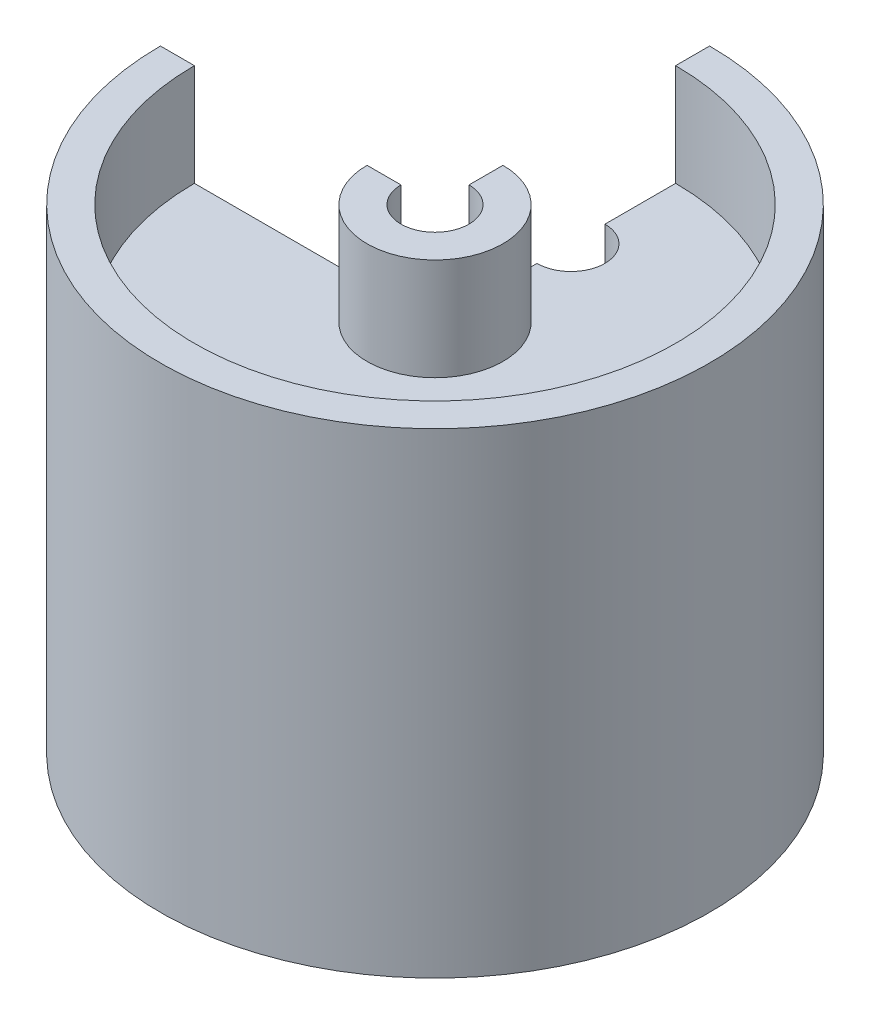
SolidWorks part; units mm, degrees
ref_plane "Front Plane" through (0, 0, 0) normal (0, 0, 1) x (1, 0, 0)
ref_plane "Top Plane" through (0, 0, 0) normal (0, 1, 0) x (1, 0, 0)
ref_plane "Right Plane" through (0, 0, 0) normal (1, 0, 0) x (0, 0, -1)
sketch "Sketch1" plane through (0, 0, 0) normal (1, 0, 0) x (0, 0, -1)
  line L3 (22.479, 35.4984) -> (22.479, 45.0234)
  line L4 (22.479, 45.0234) -> (25.654, 45.0234)
  line L5 (25.654, 45.0234) -> (25.654, 0.5734)
  line L6 (25.654, 0.5734) -> (22.479, 0.5734)
  line L7 (22.479, 0.5734) -> (22.479, 32.3234)
  line L8 (22.479, 32.3234) -> (6.35, 32.3234)
  line L12 (0, 45.0234) -> (0, 0) construction
  line L13 (22.479, 35.4984) -> (6.35, 35.4984)
  line L14 (6.35, 35.4984) -> (6.35, 45.0234)
  line L15 (6.35, 45.0234) -> (3.175, 45.0234)
  line L16 (3.175, 45.0234) -> (3.175, 0.5734)
  line L17 (3.175, 0.5734) -> (6.35, 0.5734)
  line L19 (6.35, 32.3234) -> (6.35, 0.5734)
  dimension "D1" = 44.45
  dimension "D2" = 16.129
  dimension "D3" = 3.175
  dimension "D4" = 31.75
  dimension "D5" = 16.129
  dimension "D6" = 9.525
  dimension "D7" = 3.175
revolve "Revolve2" add sketch "Sketch1" angle 270 about L12
sketch "Sketch5" plane through (0, 0, 0) normal (0, 1, 0) x (1, 0, 0)
  circle A0 centre (0, 12.7) radius 3.175
  dimension "D1" = 6.35
  dimension "D2" = 12.7
extrude "Cut-Extrude1" cut sketch "Sketch5" along normal through all
